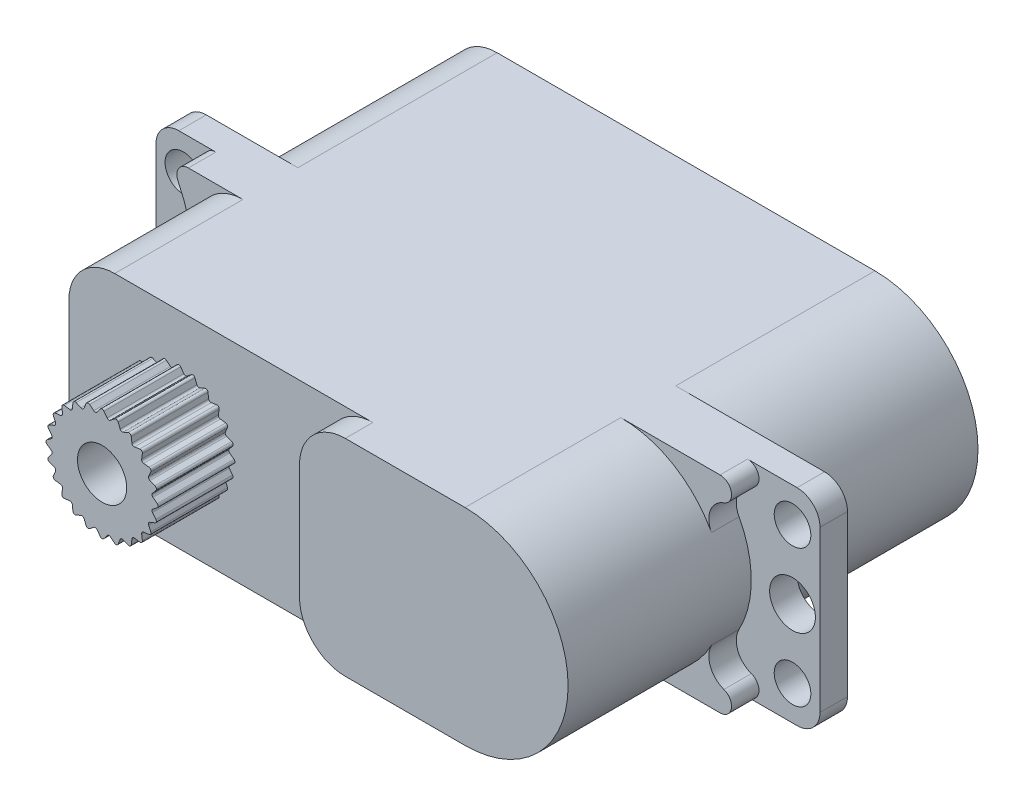
SolidWorks part; units mm, degrees
ref_plane "前视基准面" through (0, 0, 0) normal (0, 0, 1) x (1, 0, 0)
ref_plane "上视基准面" through (0, 0, 0) normal (0, 1, 0) x (1, 0, 0)
ref_plane "右视基准面" through (0, 0, 0) normal (1, 0, 0) x (0, 0, -1)
ref_plane "基准面4" through (0, 4.5, 0) normal (0, 1, 0) x (1, 0, 0)
sketch "草图1" plane through (0, 4.5, 0) normal (0, 1, 0) x (1, 0, 0)
  line L0 (-7.8, 9.9) -> (-7.8, -8)
  line L1 (-7.8, -8) -> (21.2, -8)
  line L2 (21.2, -8) -> (21.2, 9.9)
  line L3 (21.2, 9.9) -> (-7.8, 9.9)
extrude "凸台-拉伸1" add sketch "草图1" against normal blind 9
sketch "草图2" plane through (0, 0, 8) normal (0, 0, 1) x (1, 0, 0)
  line L0 (13.7, -4.5) -> (21.2, -4.5)
  line L1 (21.2, -4.5) -> (21.2, 4.5)
  line L2 (21.2, 4.5) -> (13.7, 4.5)
  arc A0 (13.7, 4.5) -> (13.7, -4.5) centre (13.7, 0) cw
extrude "切除-拉伸1" cut sketch "草图2" against normal blind 8
sketch "草图3" plane through (0, 4.5, 0) normal (0, 1, 0) x (-1, 0, 0)
  line L0 (4.8, 8) -> (4.8, 0)
  line L1 (4.8, 0) -> (7.8, 0)
  line L2 (7.8, 0) -> (7.8, 8)
  line L3 (7.8, 8) -> (4.8, 8)
extrude "切除-拉伸2" cut sketch "草图3" against normal through all
sketch "草图4" plane through (0, 0, 0) normal (0, 0, 1) x (1, 0, 0)
  line L0 (-4.8, 4.5) -> (-4.8, 0.0992)
  line L1 (-5.1837, 4.5) -> (-4.8, 4.5)
  arc A0 (-4.8, 0.0992) -> (-5.6349, 3.7845) centre (-13.3512, 0.0992) ccw
  arc A1 (-5.6349, 3.7845) -> (-5.1837, 4.5) centre (-5.1837, 4) cw
extrude "凸台-拉伸2" add sketch "草图4" along normal blind 1.2
sketch "草图5" plane through (0, 0, 0) normal (0, 0, 1) x (1, 0, 0)
  line L0 (13.7, 4.5) -> (18.0361, 4.5)
  arc A0 (18.2027, 3.5285) -> (17.6629, 2.132) centre (18.531, 2.5991) ccw
  arc A1 (17.6629, 2.132) -> (13.7, 4.5) centre (13.7, 0) ccw
  arc A2 (18.0361, 4.5) -> (18.2027, 3.5285) centre (18.0361, 4) cw
extrude "凸台-拉伸3" add sketch "草图5" along normal blind 1.2
sketch "草图6" plane through (0, 0, 0) normal (0, 0, 1) x (1, 0, 0)
  line L0 (18.0361, -4.5) -> (13.7, -4.5)
  arc A0 (17.6629, -2.132) -> (18.2027, -3.5285) centre (18.531, -2.5991) ccw
  arc A1 (18.2027, -3.5285) -> (18.0361, -4.5) centre (18.0361, -4) cw
  arc A2 (13.7, -4.5) -> (17.6629, -2.132) centre (13.7, 0) ccw
extrude "凸台-拉伸4" add sketch "草图6" along normal blind 1.2
sketch "草图7" plane through (0, 0, 0) normal (0, 0, 1) x (1, 0, 0)
  line L0 (-4.8, -0.0992) -> (-4.8, -4.5)
  line L1 (-4.8, -4.5) -> (-5.1837, -4.5)
  arc A0 (-5.6349, -3.7845) -> (-4.8, -0.0992) centre (-13.3512, -0.0992) ccw
  arc A1 (-5.1837, -4.5) -> (-5.6349, -3.7845) centre (-5.1837, -4) cw
extrude "凸台-拉伸5" add sketch "草图7" along normal blind 1.2
sketch "草图8" plane through (0, -4.5, 0) normal (0, -1, 0) x (1, 0, 0)
  line L0 (-4.8, 6.8) -> (6.4702, 6.8)
  line L1 (6.4702, 6.8) -> (6.4702, 8)
  line L2 (6.4702, 8) -> (-4.8, 8)
  line L3 (-4.8, 8) -> (-4.8, 6.8)
extrude "切除-拉伸3" cut sketch "草图8" against normal through all
sketch "草图9" plane through (0, 0, -9.9) normal (0, 0, -1) x (-1, 0, 0)
  line L0 (-21.2, -4.5) -> (-13.7, -4.5)
  line L1 (-13.7, 4.5) -> (-21.2, 4.5)
  line L2 (-21.2, 4.5) -> (-21.2, -4.5)
  arc A0 (-13.7, -4.5) -> (-13.7, 4.5) centre (-13.7, 0) cw
extrude "切除-拉伸4" cut sketch "草图9" against normal blind 8.7
sketch "草图10" plane through (0, -4.5, 0) normal (0, -1, 0) x (1, 0, 0)
  line L0 (-4.8, -9.9) -> (-4.8, -1.2)
  line L1 (-4.8, -1.2) -> (-7.8, -1.2)
  line L2 (-7.8, -1.2) -> (-7.8, -9.9)
  line L3 (-7.8, -9.9) -> (-4.8, -9.9)
extrude "切除-拉伸5" cut sketch "草图10" against normal through all
sketch "草图11" plane through (0, 0, 6.8) normal (0, 0, 1) x (1, 0, 0)
  line L0 (1.7606, 1.6469) -> (1.7104, 1.3125)
  line L1 (1.7104, 1.3125) -> (2.0464, 1.2744)
  line L2 (2.1268, 1.1351) -> (1.9919, 0.8251)
  line L3 (1.9919, 0.8251) -> (2.3065, 0.7013)
  line L4 (2.3482, 0.5459) -> (2.1375, 0.2814)
  line L5 (2.1375, 0.2814) -> (2.4094, 0.0804)
  line L6 (2.4094, -0.0804) -> (2.1375, -0.2814)
  line L7 (2.1375, -0.2814) -> (2.3482, -0.5459)
  line L8 (2.3065, -0.7013) -> (1.9919, -0.8251)
  line L9 (1.9919, -0.8251) -> (2.1268, -1.1351)
  line L10 (2.0464, -1.2744) -> (1.7104, -1.3125)
  line L11 (1.7104, -1.3125) -> (1.7606, -1.6469)
  line L12 (1.6469, -1.7606) -> (1.3125, -1.7104)
  line L13 (1.3125, -1.7104) -> (1.2744, -2.0464)
  line L14 (1.1351, -2.1268) -> (0.8251, -1.9919)
  line L15 (0.8251, -1.9919) -> (0.7013, -2.3065)
  line L16 (0.5459, -2.3482) -> (0.2814, -2.1375)
  line L17 (0.2814, -2.1375) -> (0.0804, -2.4094)
  line L18 (-0.0804, -2.4094) -> (-0.2814, -2.1375)
  line L19 (-0.2814, -2.1375) -> (-0.5459, -2.3482)
  line L20 (-0.7013, -2.3065) -> (-0.8251, -1.9919)
  line L21 (-0.8251, -1.9919) -> (-1.1351, -2.1268)
  line L22 (-1.2744, -2.0464) -> (-1.3125, -1.7104)
  line L23 (-1.3125, -1.7104) -> (-1.6469, -1.7606)
  line L24 (-1.7606, -1.6469) -> (-1.7104, -1.3125)
  line L25 (-1.7104, -1.3125) -> (-2.0464, -1.2744)
  line L26 (-2.1268, -1.1351) -> (-1.9919, -0.8251)
  line L27 (-1.9919, -0.8251) -> (-2.3065, -0.7013)
  line L28 (-2.3482, -0.5459) -> (-2.1375, -0.2814)
  line L29 (-2.1375, -0.2814) -> (-2.4094, -0.0804)
  line L30 (-2.4094, 0.0804) -> (-2.1375, 0.2814)
  line L31 (-2.1375, 0.2814) -> (-2.3482, 0.5459)
  line L32 (-2.3065, 0.7013) -> (-1.9919, 0.8251)
  line L33 (-1.9919, 0.8251) -> (-2.1268, 1.1351)
  line L34 (-2.0464, 1.2744) -> (-1.7104, 1.3125)
  line L35 (-1.7104, 1.3125) -> (-1.7606, 1.6469)
  line L36 (-1.6469, 1.7606) -> (-1.3125, 1.7104)
  line L37 (-1.3125, 1.7104) -> (-1.2744, 2.0464)
  line L38 (-1.1351, 2.1268) -> (-0.8251, 1.9919)
  line L39 (-0.8251, 1.9919) -> (-0.7013, 2.3065)
  line L40 (-0.5459, 2.3482) -> (-0.2814, 2.1375)
  line L41 (-0.2814, 2.1375) -> (-0.0804, 2.4094)
  line L42 (0.0804, 2.4094) -> (0.2814, 2.1375)
  line L43 (0.2814, 2.1375) -> (0.5459, 2.3482)
  line L44 (0.7013, 2.3065) -> (0.8251, 1.9919)
  line L45 (0.8251, 1.9919) -> (1.1351, 2.1268)
  line L46 (1.2744, 2.0464) -> (1.3125, 1.7104)
  line L47 (1.3125, 1.7104) -> (1.6469, 1.7606)
  arc A0 (1.6469, 1.7606) -> (1.7606, 1.6469) centre (1.6617, 1.6617) cw
  arc A1 (2.0464, 1.2744) -> (2.1268, 1.1351) centre (2.0352, 1.175) cw
  arc A2 (2.3065, 0.7013) -> (2.3482, 0.5459) centre (2.2699, 0.6082) cw
  arc A3 (2.4094, 0.0804) -> (2.4094, -0.0804) centre (2.35, 0) cw
  arc A4 (2.3482, -0.5459) -> (2.3065, -0.7013) centre (2.2699, -0.6082) cw
  arc A5 (2.1268, -1.1351) -> (2.0464, -1.2744) centre (2.0352, -1.175) cw
  arc A6 (1.7606, -1.6469) -> (1.6469, -1.7606) centre (1.6617, -1.6617) cw
  arc A7 (1.2744, -2.0464) -> (1.1351, -2.1268) centre (1.175, -2.0352) cw
  arc A8 (0.7013, -2.3065) -> (0.5459, -2.3482) centre (0.6082, -2.2699) cw
  arc A9 (0.0804, -2.4094) -> (-0.0804, -2.4094) centre (0, -2.35) cw
  arc A10 (-0.5459, -2.3482) -> (-0.7013, -2.3065) centre (-0.6082, -2.2699) cw
  arc A11 (-1.1351, -2.1268) -> (-1.2744, -2.0464) centre (-1.175, -2.0352) cw
  arc A12 (-1.6469, -1.7606) -> (-1.7606, -1.6469) centre (-1.6617, -1.6617) cw
  arc A13 (-2.0464, -1.2744) -> (-2.1268, -1.1351) centre (-2.0352, -1.175) cw
  arc A14 (-2.3065, -0.7013) -> (-2.3482, -0.5459) centre (-2.2699, -0.6082) cw
  arc A15 (-2.4094, -0.0804) -> (-2.4094, 0.0804) centre (-2.35, 0) cw
  arc A16 (-2.3482, 0.5459) -> (-2.3065, 0.7013) centre (-2.2699, 0.6082) cw
  arc A17 (-2.1268, 1.1351) -> (-2.0464, 1.2744) centre (-2.0352, 1.175) cw
  arc A18 (-1.7606, 1.6469) -> (-1.6469, 1.7606) centre (-1.6617, 1.6617) cw
  arc A19 (-1.2744, 2.0464) -> (-1.1351, 2.1268) centre (-1.175, 2.0352) cw
  arc A20 (-0.7013, 2.3065) -> (-0.5459, 2.3482) centre (-0.6082, 2.2699) cw
  arc A21 (-0.0804, 2.4094) -> (0.0804, 2.4094) centre (0, 2.35) cw
  arc A22 (0.5459, 2.3482) -> (0.7013, 2.3065) centre (0.6082, 2.2699) cw
  arc A23 (1.1351, 2.1268) -> (1.2744, 2.0464) centre (1.175, 2.0352) cw
extrude "凸台-拉伸6" add sketch "草图11" along normal blind 3.35
hole_wizard "Ø4.9 (4.9) 直径孔1" positions "草图13" profile "草图12" hole size "Ø4.9" standard "ANSI Metric"
sketch "草图13" plane through (0, 0, -9.9) normal (0, 0, -1) x (-1, 0, 0)
  point P0 (0, 0)
sketch "草图12" plane through (0, 0, -9.9) normal (1, 0, 0) x (0, 1, 0)
  line L0 (0, 0) -> (0, 8.7)
  line L1 (0, 8.7) -> (2.45, 8.7)
  line L2 (2.45, 8.7) -> (2.45, 0)
  line L5 (2.45, 0) -> (0, 0)
  line L10 (0, 8.7) -> (-2.45, 8.7) construction
  line L11 (0, -6.35) -> (0, 107.95) construction
  dimension "孔直径" = 4.9
  dimension "孔深度" = 8.7
  dimension "导头角度" = 180
hole_wizard "Ø2.0 (2) 直径孔1" positions "草图15" profile "草图14" hole size "Ø2.0" standard "ANSI Metric"
sketch "草图15" plane through (0, 0, -1.2) normal (0, 0, -1) x (-1, 0, 0)
  point P0 (6.6, 0)
  point P1 (-20, 0)
sketch "草图14" plane through (-6.6, 0, -1.2) normal (1, 0, 0) x (0, 1, 0)
  line L0 (0, 0) -> (0, 11.35)
  line L1 (0, 11.35) -> (1, 11.35)
  line L2 (1, 11.35) -> (1, 0)
  line L5 (1, 0) -> (0, 0)
  line L11 (0, -6.35) -> (0, 107.95) construction
  dimension "通孔孔直径" = 2
  dimension "通孔孔深度" = 11.35
hole_wizard "Ø1.6 (1.6) 直径孔1" positions "草图17" profile "草图16" hole size "Ø1.6" standard "ANSI Metric"
sketch "草图17" plane through (0, 0, -1.2) normal (0, 0, -1) x (-1, 0, 0)
  point P0 (6.6, -3)
  point P1 (6.6, 3)
  point P2 (-20, -3)
  point P3 (-20, 3)
sketch "草图16" plane through (-6.6, -3, -1.2) normal (1, 0, 0) x (0, 1, 0)
  line L0 (0, 0) -> (0, 11.35)
  line L1 (0, 11.35) -> (0.8, 11.35)
  line L2 (0.8, 11.35) -> (0.8, 0)
  line L5 (0.8, 0) -> (0, 0)
  line L11 (0, -6.35) -> (0, 107.95) construction
  dimension "通孔孔直径" = 1.6
  dimension "通孔孔深度" = 11.35
hole_wizard "Ø2.15 (2.15) 直径孔1" positions "草图19" profile "草图18" hole size "Ø2.15" standard "ANSI Metric"
sketch "草图19" plane through (0, 0, 10.15) normal (0, 0, 1) x (1, 0, 0)
  point P0 (0, 0)
sketch "草图18" plane through (0, 0, 10.15) normal (1, 0, 0) x (0, -1, 0)
  line L0 (0, 0) -> (0, 4.6959)
  line L1 (0, 4.6959) -> (1.075, 4.05)
  line L2 (1.075, 4.05) -> (1.075, 0)
  line L5 (1.075, 0) -> (0, 0)
  line L10 (0, 4.6959) -> (-1.075, 4.05) construction
  line L11 (0, -6.35) -> (0, 107.95) construction
  dimension "孔直径" = 2.15
  dimension "孔深度" = 4.05
  dimension "导头角度" = 118
fillet "圆角1" radius 0.1 24 edges at (1.7104, -1.3125, 8.475) (0.8251, -1.9919, 8.475) (2.1375, -0.2814, 8.475) (-1.7104, 1.3125, 8.475) (1.3125, -1.7104, 8.475) (1.9919, 0.8251, 8.475) (1.9919, -0.8251, 8.475) (-0.8251, -1.9919, 8.475) (2.1375, 0.2814, 8.475) (0.2814, -2.1375, 8.475) (-1.7104, -1.3125, 8.475) (-0.8251, 1.9919, 8.475) (-1.9919, -0.8251, 8.475) (1.3125, 1.7104, 8.475) (-2.1375, -0.2814, 8.475) (-0.2814, 2.1375, 8.475) (-2.1375, 0.2814, 8.475) (0.8251, 1.9919, 8.475) (-1.9919, 0.8251, 8.475) (-1.3125, -1.7104, 8.475) (0.2814, 2.1375, 8.475) (-1.3125, 1.7104, 8.475) (-0.2814, -2.1375, 8.475) (1.7104, 1.3125, 8.475)
fillet "圆角2" radius 1 4 edges at (-7.8, -4.5, -0.6) (-7.8, 4.5, -0.6) (21.2, 4.5, -0.6) (21.2, -4.5, -0.6)
fillet "圆角3" radius 2 6 edges at (6.4702, -4.5, 7.4) (6.4702, 4.5, 7.4) (-4.8, -4.5, 4) (-4.8, 4.5, 4) (-4.8, -4.5, -5.55) (-4.8, 4.5, -5.55)
